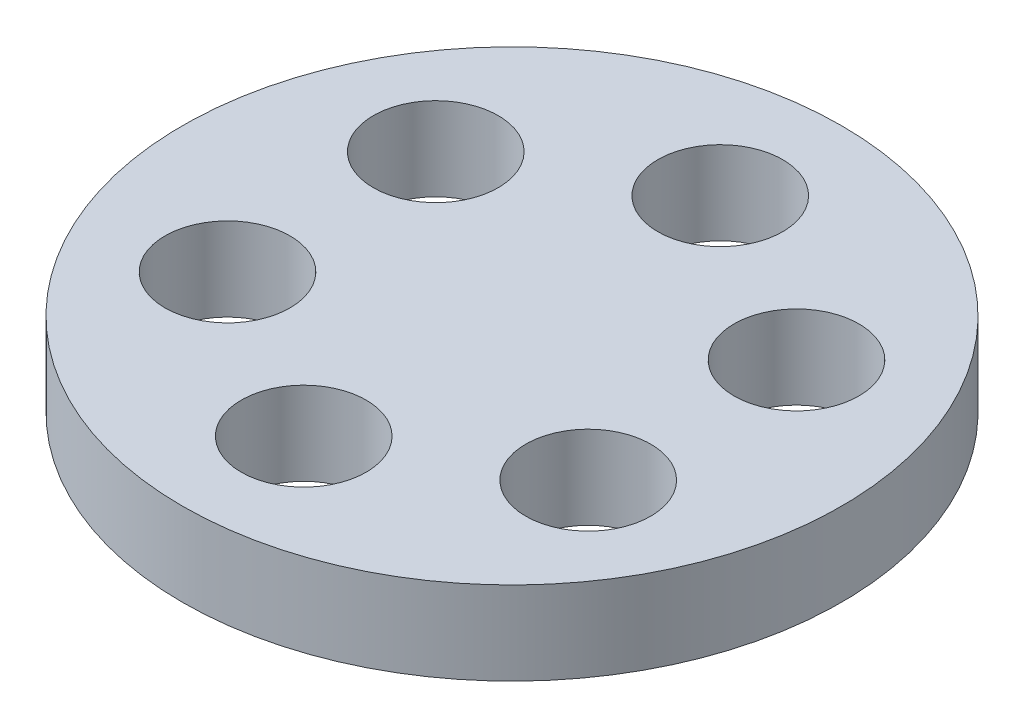
SolidWorks part; units mm, degrees
material "Epoxy, Unfilled"
ref_plane "Front Plane" through (0, 0, 0) normal (0, 0, 1) x (1, 0, 0)
ref_plane "Top Plane" through (0, 0, 0) normal (0, 1, 0) x (1, 0, 0)
ref_plane "Right Plane" through (0, 0, 0) normal (1, 0, 0) x (0, 0, -1)
sketch "Sketch3" plane through (0, 0, 0) normal (0, 1, 0) x (1, 0, 0)
  line L0 (0, 0) -> (0, 31.75)
  circle A1 centre (0, 0) radius 50.2412
  circle A2 centre (0, 31.75) radius 9.525
  circle A3 centre (27.4963, 15.875) radius 9.525
  circle A4 centre (27.4963, -15.875) radius 9.525
  circle A5 centre (0, -31.75) radius 9.525
  circle A6 centre (-27.4963, -15.875) radius 9.525
  circle A7 centre (-27.4963, 15.875) radius 9.525
extrude "Boss-Extrude1" add sketch "Sketch3" along normal blind 12.7
